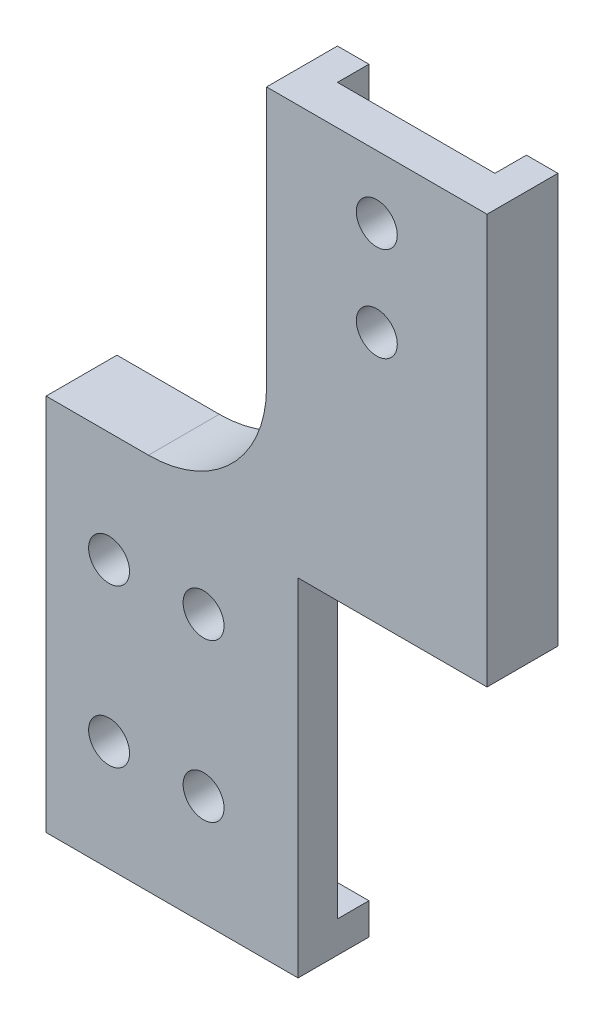
SolidWorks part; units mm, degrees
ref_plane "Front Plane" through (0, 0, 0) normal (0, 0, 1) x (1, 0, 0)
ref_plane "Top Plane" through (0, 0, 0) normal (0, 1, 0) x (1, 0, 0)
ref_plane "Right Plane" through (0, 0, 0) normal (1, 0, 0) x (0, 0, -1)
sketch "Sketch1" plane through (0, 0, 0) normal (0, 0, 1) x (1, 0, 0)
  line L0 (-39.1632, 11.4893) -> (-39.1632, -36.5107)
  line L1 (-39.1632, -36.5107) -> (16.8368, -36.5107)
  line L2 (16.8368, -36.5107) -> (16.8368, 59.4893)
  line L3 (16.8368, 59.4893) -> (-11.1632, 59.4893)
  line L4 (-11.1632, 59.4893) -> (-11.1632, 11.4893)
  line L5 (-11.1632, 11.4893) -> (-39.1632, 11.4893)
  line L6 (-39.597, -22.5107) -> (16.8368, -22.5107) construction
  line L7 (2.8368, 59.4893) -> (2.8368, -36.5107) construction
  line L8 (-11.1632, 11.4893) -> (16.8368, 11.4893) construction
  line L9 (-11.1632, 11.4893) -> (-11.1632, -36.5107) construction
  line L10 (-39.1632, -2.5107) -> (16.8368, -2.5107) construction
  line L11 (16.8368, -36.5107) -> (-7.1632, -36.5107)
  line L12 (-7.1632, -36.5107) -> (-7.1632, 7.4893)
  line L13 (-7.1632, 7.4893) -> (16.8368, 7.4893)
  line L14 (16.8368, 7.4893) -> (16.8368, -36.5107)
  circle A0 centre (-31.1632, -22.5107) radius 2.6
  circle A1 centre (-19.1632, -22.5107) radius 2.6
  circle A2 centre (2.8368, 51.4893) radius 2.6
  circle A3 centre (2.8368, 39.4893) radius 2.6
  circle A4 centre (-31.1632, -2.5107) radius 2.6
  circle A5 centre (-19.1632, -2.5107) radius 2.6
  dimension "D1" = 5.2
  dimension "D2" = 8
  dimension "D3" = 8
  dimension "D4" = 12
  dimension "D5" = 48
  dimension "D6" = 14
  dimension "D7" = 20
  dimension "D8" = 28
  dimension "D9" = 8
  dimension "D10" = 12
  dimension "D11" = 28
  dimension "D12" = 44
  dimension "D13" = 24
extrude "Boss-Extrude1" add sketch "Sketch1" along normal blind 5 contours L12 L13 L2 L3 L4 L5 L0 L1 A5 A4 A3 A2 A1 A0
sketch "Sketch3" plane through (0, 0, 0) normal (0, 0, -1) x (-1, 0, 0)
  line L0 (7.1632, -36.5107) -> (7.1632, 7.4893) construction
  line L1 (39.1632, -36.5107) -> (7.1632, -36.5107)
  line L2 (39.1632, -36.5107) -> (39.1632, -32.5107)
  line L3 (39.1632, -32.5107) -> (7.1632, -32.5107)
  line L4 (7.1632, -36.5107) -> (7.1632, -32.5107)
  line L5 (39.1632, 11.4893) -> (39.1632, -36.5107) construction
  line L6 (11.1632, 11.4893) -> (39.1632, 11.4893)
  line L7 (11.1632, 11.4893) -> (11.1632, 7.4893)
  line L8 (11.1632, 7.4893) -> (39.1632, 7.4893)
  line L9 (39.1632, 11.4893) -> (39.1632, 7.4893)
  line L10 (7.1632, 7.4893) -> (-16.8368, 7.4893) construction
  line L11 (-16.8368, 59.4893) -> (-12.8368, 59.4893)
  line L12 (-16.8368, 59.4893) -> (-16.8368, 7.4893)
  line L13 (-16.8368, 7.4893) -> (-12.8368, 7.4893)
  line L14 (-12.8368, 59.4893) -> (-12.8368, 7.4893)
  line L15 (-16.8368, 59.4893) -> (11.1632, 59.4893) construction
  line L16 (11.1632, 11.4893) -> (7.1632, 11.4893)
  line L17 (11.1632, 11.4893) -> (11.1632, 59.4893)
  line L18 (11.1632, 59.4893) -> (7.1632, 59.4893)
  line L19 (7.1632, 11.4893) -> (7.1632, 59.4893)
  line L20 (7.1632, 11.4893) -> (7.1632, 7.4893)
  line L21 (11.1632, 11.4893) -> (7.1632, 11.4893)
  line L22 (11.1632, 7.4893) -> (11.1632, 11.4893)
  line L23 (7.1632, 7.4893) -> (11.1632, 7.4893)
  dimension "D1" = 4
  dimension "D2" = 4
  dimension "D3" = 4
  dimension "D4" = 4
extrude "Boss-Extrude3" add sketch "Sketch3" along normal blind 4
fillet "Fillet1" radius 15 1 edges at (-11.1632, 11.4893, 0.5)
